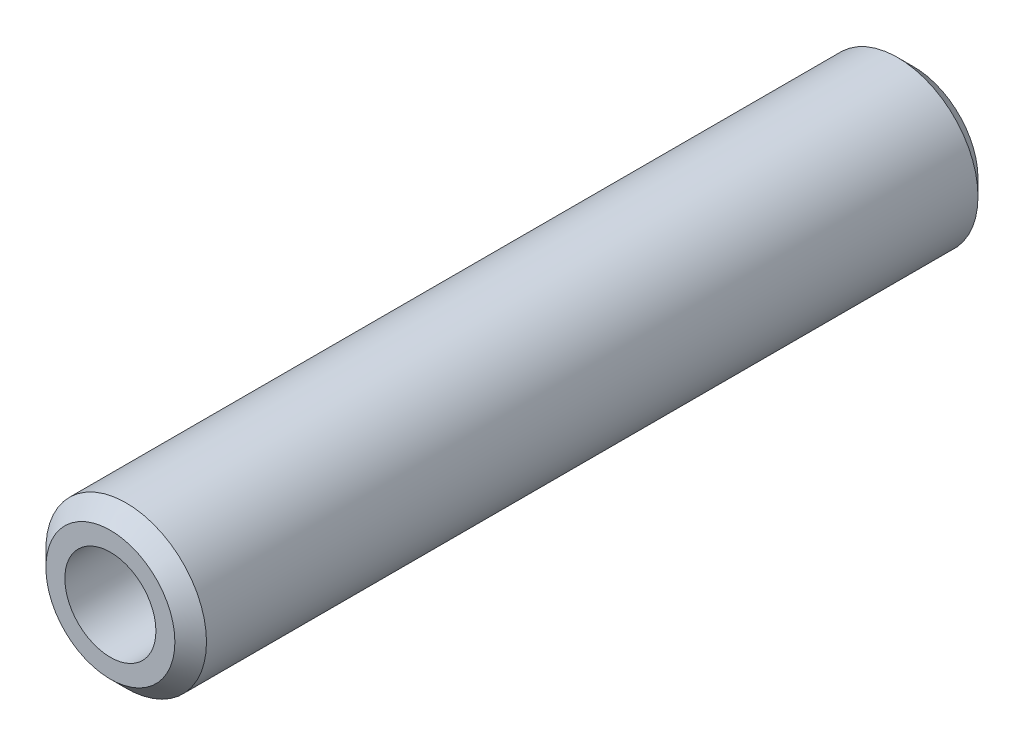
SolidWorks part; units mm, degrees
ref_plane "Front Plane" through (0, 0, 0) normal (0, 0, 1) x (1, 0, 0)
ref_plane "Top Plane" through (0, 0, 0) normal (0, 1, 0) x (1, 0, 0)
ref_plane "Right Plane" through (0, 0, 0) normal (1, 0, 0) x (0, 0, -1)
sketch "Sketch1" plane through (0, 0, 0) normal (0, 0, 1) x (1, 0, 0)
  circle A0 centre (0, 0) radius 7.2
  circle A1 centre (0, 0) radius 12.7
  dimension "D1" = 25.4
  dimension "D2" = 5.5
extrude "Boss-Extrude1" add sketch "Sketch1" along normal mid plane 127
chamfer "Chamfer1" distance 2.5 angle 45 2 edges at (12.7, 0, -63.5) (12.7, 0, 63.5)
